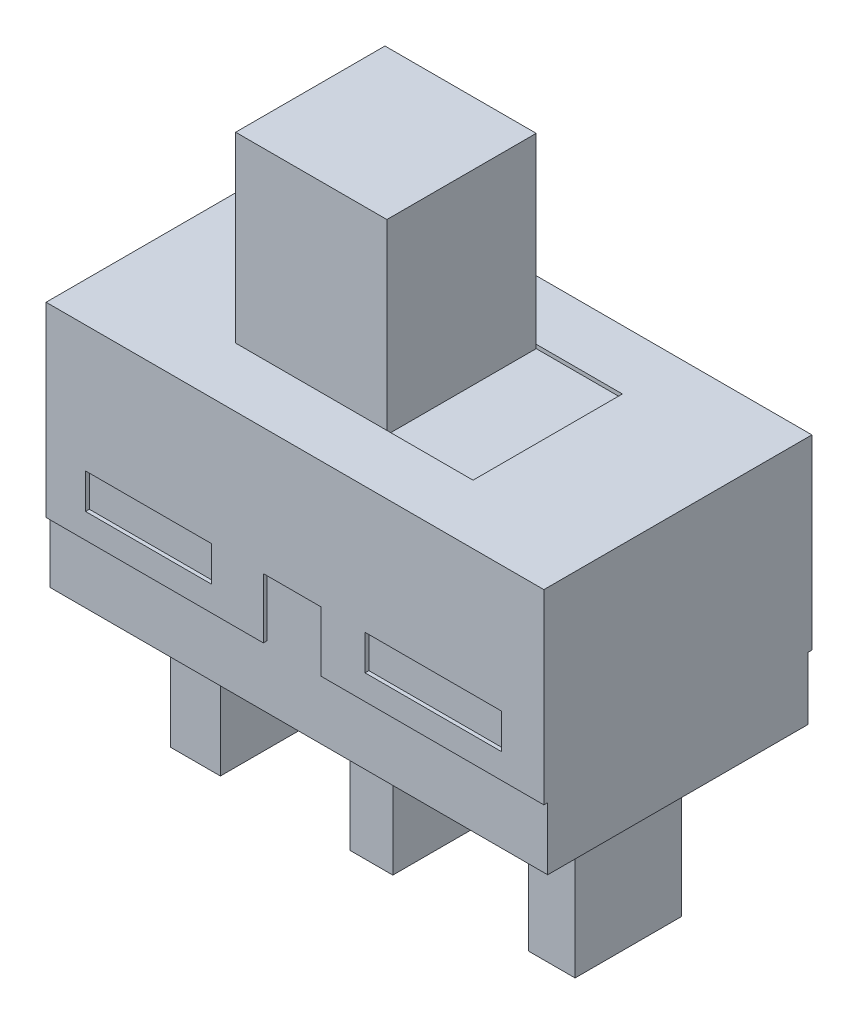
SolidWorks part; units mm, degrees
ref_plane "Front Plane" through (0, 0, 0) normal (0, 0, 1) x (1, 0, 0)
ref_plane "Top Plane" through (0, 0, 0) normal (0, 1, 0) x (1, 0, 0)
ref_plane "Right Plane" through (0, 0, 0) normal (1, 0, 0) x (0, 0, -1)
sketch "Sketch1" plane through (0, 0, 0) normal (0, 1, 0) x (1, 0, 0)
  line L1 (-6.0244, 5.426) -> (6.9756, 5.426)
  line L2 (-6.0244, 5.426) -> (-6.0244, -1.374)
  line L3 (-6.0244, -1.374) -> (6.9756, -1.374)
  line L4 (6.9756, 5.426) -> (6.9756, -1.374)
  dimension "D1" = 13
  dimension "D2" = 6.8
extrude "Boss-Extrude1" add sketch "Sketch1" along normal blind 6.4
sketch "Sketch2" plane through (0, 0, 1.374) normal (0, 0, 1) x (1, 0, 0)
  line L0 (6.9756, 6.4) -> (6.9756, 0) construction
  line L1 (-6.0244, 6.4) -> (6.9756, 6.4)
  line L2 (-6.0244, 6.4) -> (-6.0244, 1.6313)
  line L3 (-6.0244, 1.6313) -> (6.9756, 1.6313)
  line L4 (6.9756, 6.4) -> (6.9756, 1.6313)
  line L6 (-0.3515, 3.2) -> (1.1532, 3.2)
  line L7 (-0.3515, 3.2) -> (-0.3515, 1.2364)
  line L8 (-0.3515, 1.2364) -> (1.1532, 1.2364)
  line L9 (1.1532, 3.2) -> (1.1532, 1.2364)
  line L10 (-4.9937, 3.2) -> (-1.7068, 3.2)
  line L11 (-4.9937, 3.2) -> (-4.9937, 2.2822)
  line L12 (-4.9937, 2.2822) -> (-1.7068, 2.2822)
  line L13 (-1.7068, 3.2) -> (-1.7068, 2.2822)
  line L14 (2.3058, 3.2) -> (5.8701, 3.2)
  line L15 (2.3058, 3.2) -> (2.3058, 2.2822)
  line L16 (2.3058, 2.2822) -> (5.8701, 2.2822)
  line L17 (5.8701, 3.2) -> (5.8701, 2.2822)
  line M2 (6.9756, 0) -> (6.9756, 6.4)
  line M3 (6.9756, 6.4) -> (-6.0244, 6.4)
  line M4 (-6.0244, 6.4) -> (-6.0244, 0)
extrude "Boss-Extrude2" add sketch "Sketch2" against normal blind 6.9 and the other way blind 0.1 contours L6 L9 L3 L7 L10 L13 L12 L11 L14 L17 L16 L15 M2 M3 M4
sketch "Sketch3" plane through (0, 6.4, 0) normal (0, 1, 0) x (1, 0, 0)
  line L1 (-2.6244, 3.976) -> (3.5756, 3.976)
  line L2 (-2.6244, 3.976) -> (-2.6244, 0.076)
  line L3 (-2.6244, 0.076) -> (3.5756, 0.076)
  line L4 (-6.0244, 5.526) -> (-6.0244, -1.474)
  line L5 (-6.0244, -1.474) -> (6.9756, -1.474)
  line L6 (6.9756, -1.474) -> (6.9756, 5.526)
  line L7 (6.9756, 5.526) -> (-6.0244, 5.526)
  line L8 (-6.0244, 5.526) -> (-6.0244, -1.474)
  line L9 (-6.0244, -1.474) -> (6.9756, -1.474)
  line L10 (6.9756, -1.474) -> (6.9756, 5.526)
  line L11 (6.9756, 5.526) -> (-6.0244, 5.526)
  line L12 (3.5756, 3.976) -> (3.5756, 0.076)
  dimension "D2" = 6.2
  dimension "D3" = 3.9
  dimension "D4" = 1.55
  dimension "D5" = 3.4
  dimension "D1" = 0
extrude "Boss-Extrude3" add sketch "Sketch3" along normal blind 0.1
sketch "Sketch4" plane through (0, 6.4, 0) normal (0, 1, 0) x (1, 0, 0)
  line L0 (-2.6244, 0.076) -> (3.5756, 0.076) construction
  line L1 (-2.6244, 3.976) -> (1.3256, 3.976)
  line L2 (-2.6244, 3.976) -> (-2.6244, 0.076)
  line L3 (-2.6244, 0.076) -> (1.3256, 0.076)
  line L4 (1.3256, 3.976) -> (1.3256, 0.076)
  line L5 (3.5756, 0.076) -> (3.5756, 3.976) construction
  dimension "D1" = 2.25
extrude "Boss-Extrude4" add sketch "Sketch4" along normal blind 4.87
sketch "Sketch5" plane through (0, 0, 0) normal (0, -1, 0) x (1, 0, 0)
  line L1 (-0.1601, -0.596) -> (0.9611, -0.596)
  line L2 (-0.1601, -0.596) -> (-0.1601, -3.3706)
  line L3 (-0.1601, -3.3706) -> (0.9611, -3.3706)
  line L4 (0.9611, -0.596) -> (0.9611, -3.3706)
  line L5 (-4.8336, -0.5853) -> (-3.5317, -0.5853)
  line L6 (-4.8336, -0.5853) -> (-4.8336, -3.424)
  line L7 (-4.8336, -3.424) -> (-3.5317, -3.424)
  line L8 (-3.5317, -0.5853) -> (-3.5317, -3.424)
  line L9 (4.4508, -0.6493) -> (5.6674, -0.6493)
  line L10 (4.4508, -0.6493) -> (4.4508, -3.424)
  line L11 (4.4508, -3.424) -> (5.6674, -3.424)
  line L12 (5.6674, -0.6493) -> (5.6674, -3.424)
extrude "Boss-Extrude5" add sketch "Sketch5" along normal blind 4
